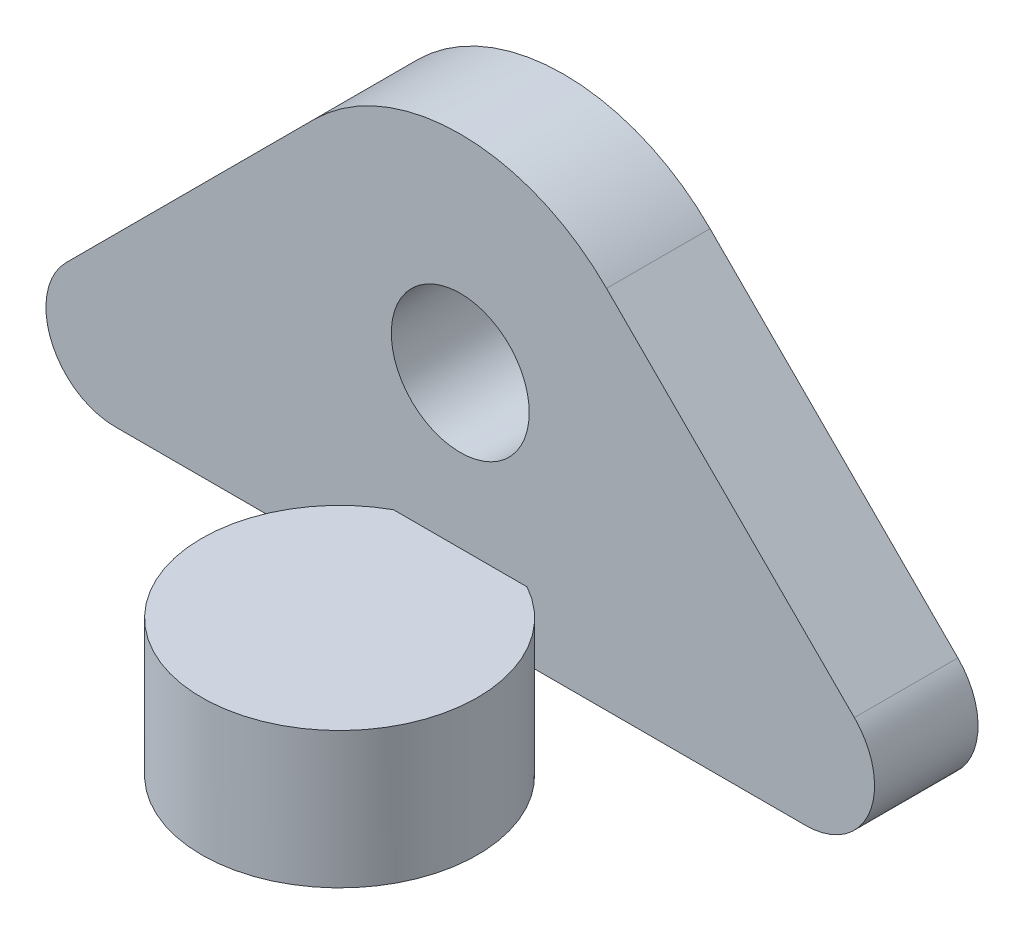
SolidWorks part; units mm, degrees
material "AISI 1035 Steel (SS)"
ref_plane "Front Plane" through (0, 0, 0) normal (0, 0, 1) x (1, 0, 0)
ref_plane "Top Plane" through (0, 0, 0) normal (0, 1, 0) x (1, 0, 0)
ref_plane "Right Plane" through (0, 0, 0) normal (1, 0, 0) x (0, 0, -1)
sketch "Sketch1" plane through (0, 0, 0) normal (0, 0, 1) x (1, 0, 0)
  line L3 (-8.0772, -5.1283) -> (8.0772, -5.1283)
  line L4 (-9.2177, -2.3749) -> (-3.4215, 3.4214)
  line L5 (3.4215, 3.4214) -> (9.2177, -2.3749)
  circle A0 centre (0, 0) radius 1.6129
  arc A2 (8.0772, -5.1283) -> (9.2177, -2.3749) centre (8.0772, -3.5154) ccw
  arc A3 (-9.2177, -2.3749) -> (-8.0772, -5.1283) centre (-8.0772, -3.5154) ccw
  arc A4 (3.4215, 3.4214) -> (-3.4215, 3.4214) centre (0, 0) ccw
extrude "Boss-Extrude1" add sketch "Sketch1" against normal blind 2.4206
sketch "Sketch2" plane through (0, -5.1283, 0) normal (0, -1, 0) x (1, 0, 0)
  line L0 (-8.0772, 0) -> (8.0772, 0) construction
  circle A0 centre (0, 2.8219) radius 3.2258
  dimension "D1" = 2.8219
extrude "Boss-Extrude2" add sketch "Sketch2" along normal blind 1.6129 and the other way blind 1.5748
sketch "Sketch3" plane through (0, -6.7412, 0) normal (0, -1, 0) x (1, 0, 0)
  circle A0 centre (0, 2.8219) radius 2.4206
extrude "Cut-Extrude1" cut sketch "Sketch3" against normal blind 2.4206
